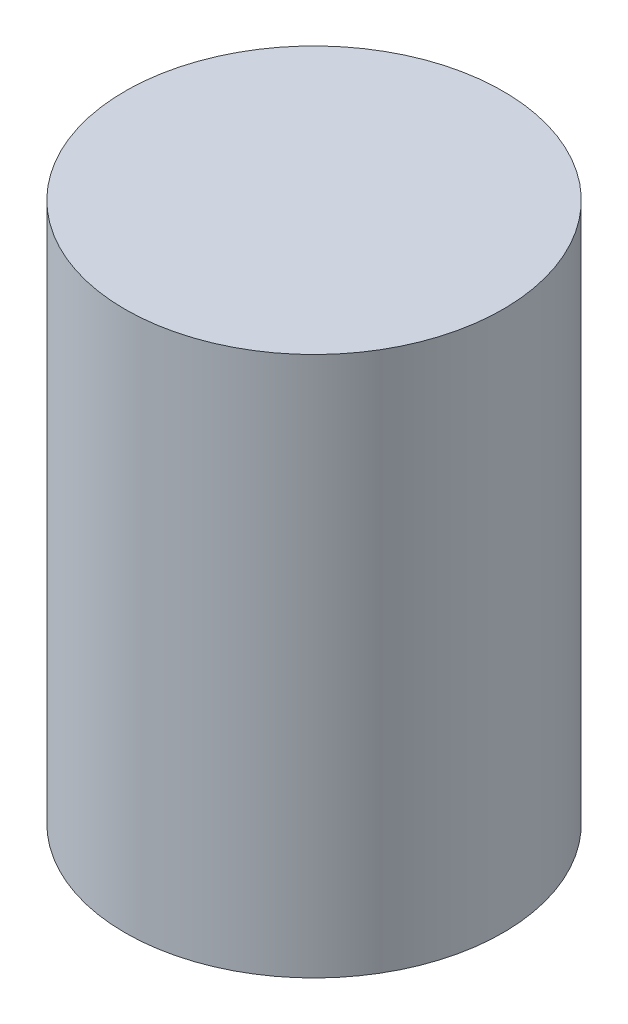
SolidWorks part; units mm, degrees
ref_plane "Front Plane" through (0, 0, 0) normal (0, 0, 1) x (1, 0, 0)
ref_plane "Top Plane" through (0, 0, 0) normal (0, 1, 0) x (1, 0, 0)
ref_plane "Right Plane" through (0, 0, 0) normal (1, 0, 0) x (0, 0, -1)
sketch "Sketch1" plane through (0, 0, 0) normal (0, 1, 0) x (1, 0, 0)
  circle A0 centre (0, 0) radius 0.7
extrude "Boss-Extrude1" add sketch "Sketch1" along normal blind 2
